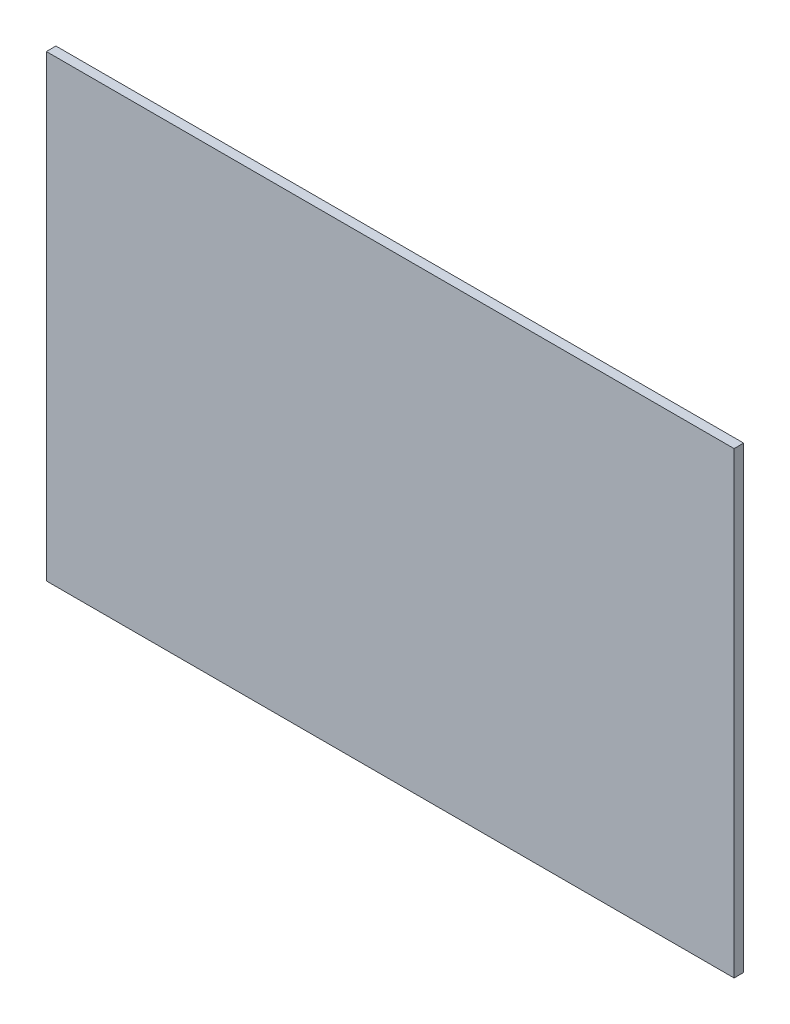
SolidWorks part; units mm, degrees
material "Pine"
ref_plane "Front" through (0, 0, 0) normal (0, 0, 1) x (1, 0, 0)
ref_plane "Top" through (0, 0, 0) normal (0, 1, 0) x (1, 0, 0)
ref_plane "Right" through (0, 0, 0) normal (1, 0, 0) x (0, 0, -1)
sketch "Sketch1" plane through (0, 0, 0) normal (0, 0, 1) x (1, 0, 0)
  line L1 (-104.7161, 1145.4367) -> (1724.0839, 1145.4367)
  line L2 (-104.7161, 1145.4367) -> (-104.7161, -73.7633)
  line L3 (-104.7161, -73.7633) -> (1724.0839, -73.7633)
  line L4 (1724.0839, 1145.4367) -> (1724.0839, -73.7633)
extrude "Extrude1" add sketch "Sketch1" along normal blind 25.4
